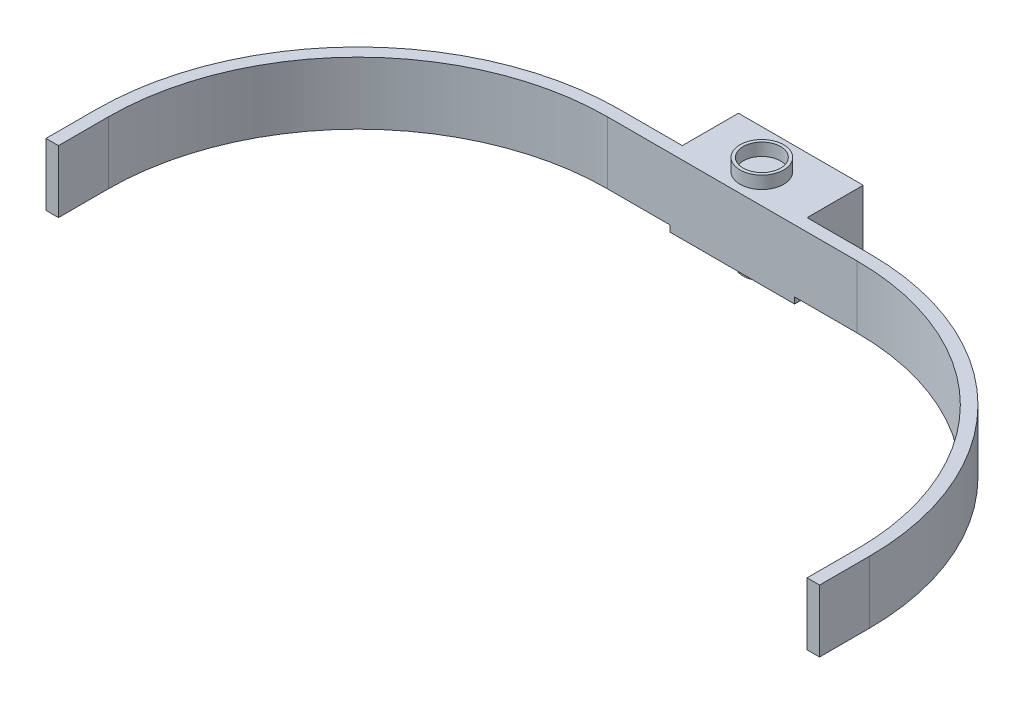
SolidWorks part; units mm, degrees
ref_plane "Front" through (0, 0, 0) normal (0, 0, 1) x (1, 0, 0)
ref_plane "Top" through (0, 0, 0) normal (0, 1, 0) x (1, 0, 0)
ref_plane "Right" through (0, 0, 0) normal (1, 0, 0) x (0, 0, -1)
sketch "草图2" plane through (0, 0, 0) normal (1, 0, 0) x (0, 0, -1)
  line L0 (0, 0) -> (-13.2631, 0) construction
  line L1 (-10, 1) -> (10, 1)
  line L3 (-10, -1) -> (10, -1)
  line L5 (0, 0) -> (0, 8.7818) construction
  line L6 (-18.7262, 30) -> (26.9936, 30) construction
  line L7 (10, 1) -> (10, -1)
  line L21 (-10, -1) -> (-12, -1)
  line L22 (-10, 1) -> (-12, 1)
  line L25 (-12, 1) -> (-12, -1)
  dimension "D1" = 1
  dimension "D2" = 2
  dimension "D3" = 20
  dimension "D5" = 30
extrude "凸台-拉伸1" add sketch "草图2" along normal mid plane 40
sketch "草图9" plane through (0, 1, 0) normal (0, 1, 0) x (1, 0, 0)
  line L0 (0, 10) -> (0, 6) construction
  line L2 (-20, -12) -> (46.4824, -12) construction
  line L3 (0, -12) -> (0, -115.9508) construction
  line L6 (-105.6347, -92) -> (112.3187, -92) construction
  line L11 (-40, -92) -> (40, -92) construction
  line L20 (-40, -8) -> (40, -8)
  line L22 (-40, -92) -> (40, -92) construction
  line L23 (-40, -12) -> (40, -12)
  line L29 (-124, -92) -> (-124, -108)
  line L30 (-124, -108) -> (-120, -108)
  line L31 (-120, -92) -> (-120, -108)
  line L33 (120, -92) -> (120, -108)
  line L34 (120, -108) -> (124, -108)
  line L35 (124, -92) -> (124, -108)
  arc A4 (-40, -8) -> (-124, -92) centre (-40, -92) ccw
  arc A5 (124, -92) -> (40, -8) centre (40, -92) ccw
  arc A6 (-40, -12) -> (-120, -92) centre (-40, -92) ccw
  arc A7 (120, -92) -> (40, -12) centre (40, -92) ccw
  point P7 (0, -92)
  point P10 (0, -92)
  point P13 (0, -92)
  point P19 (0, -92)
  dimension "D2" = 16
  dimension "D1" = 80
  dimension "D3" = 16
extrude "凸台-拉伸4" add sketch "草图9" along normal blind 20
sketch "草图10" plane through (0, 1, 0) normal (0, 1, 0) x (1, 0, 0)
  line L1 (-20, 10) -> (20, 10)
  line L2 (-20, 10) -> (-20, -8)
  line L3 (-20, -8) -> (20, -8)
  line L4 (20, 10) -> (20, -8)
extrude "凸台-拉伸5" add sketch "草图10" along normal blind 20
sketch "草图11" plane through (0, 21, 0) normal (0, 1, 0) x (1, 0, 0)
  line L0 (0, -12) -> (0, 10) construction
  line L1 (-40, -12) -> (40, -12) construction
  line L2 (20, 10) -> (-20, 10) construction
  circle A0 centre (0, -2.5) radius 6
  circle A1 centre (0, -2.5) radius 7
  dimension "D1" = 9.5
extrude "凸台-拉伸6" add sketch "草图11" along normal blind 4
sketch "草图12" plane through (0, -1, 0) normal (0, -1, 0) x (1, 0, 0)
  line L0 (0, 0) -> (0, 17.62) construction
  line L1 (20, 12) -> (-20, 12) construction
  circle A0 centre (0, 2.5) radius 6
  dimension "D1" = 9.5
extrude "凸台-拉伸7" add sketch "草图12" along normal blind 4
